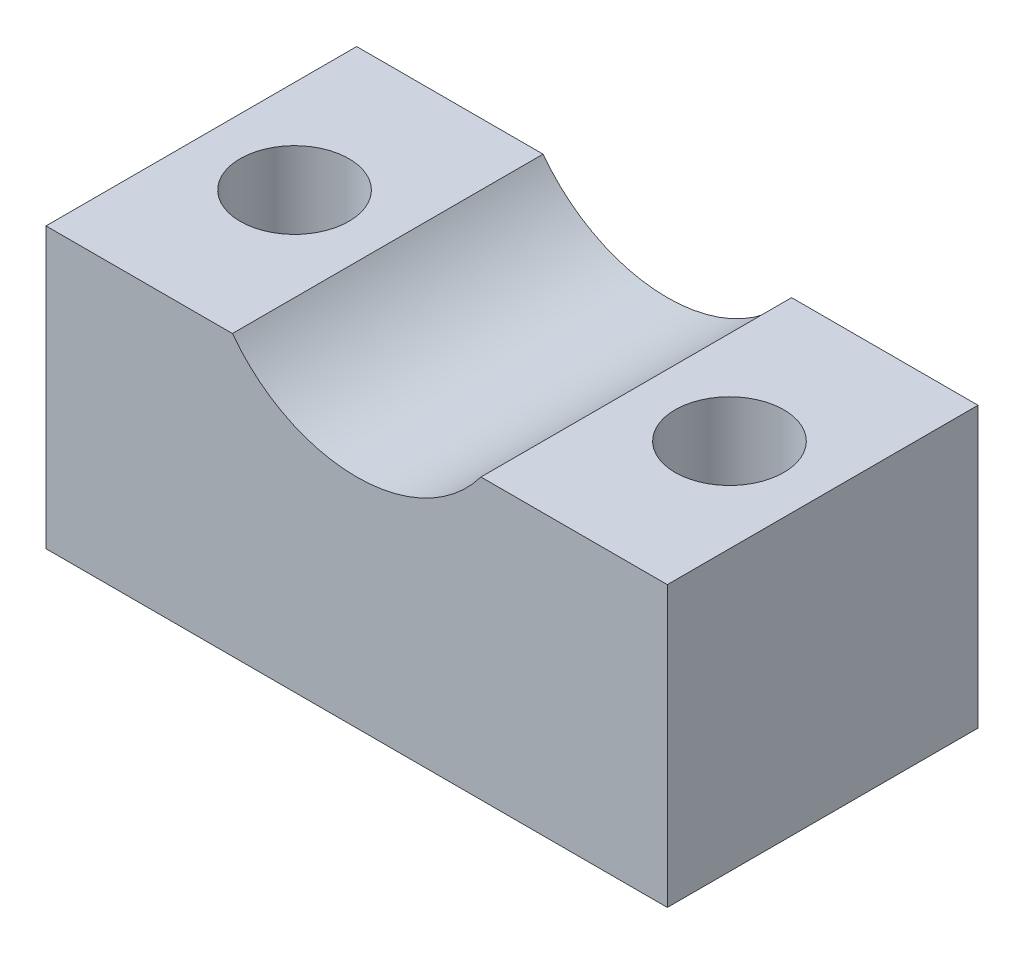
SolidWorks part; units mm, degrees
ref_plane "Ebene vorne" through (0, 0, 0) normal (0, 0, 1) x (1, 0, 0)
ref_plane "Ebene oben" through (0, 0, 0) normal (0, 1, 0) x (1, 0, 0)
ref_plane "Ebene rechts" through (0, 0, 0) normal (1, 0, 0) x (0, 0, -1)
sketch "Skizze1" plane through (0, 0, 0) normal (0, 0, 1) x (1, 0, 0)
  line L0 (0, 0) -> (20, 0)
  line L1 (20, 0) -> (20, 9)
  line L2 (20, 9) -> (14, 9)
  line L3 (0, 0) -> (0, 9)
  line L4 (0, 9) -> (6, 9)
  arc A0 (6, 9) -> (14, 9) centre (10, 12) ccw
  point P7 (10, 7)
  dimension "D1" = 6
  dimension "D2" = 6
  dimension "D3" = 2
  dimension "D4" = 9
  dimension "D5" = 20
  dimension "D6" = 0
  dimension "D7" = 0
  dimension "D8" = 0
extrude "Aufsatz-Linear austragen1" add sketch "Skizze1" along normal blind 10
sketch "Skizze2" plane through (0, 9, 0) normal (0, 1, 0) x (1, 0, 0)
  line L0 (6, 0) -> (0, 0) construction
  line L1 (0, -10) -> (0, 0) construction
  line L2 (20, -10) -> (20, 0) construction
  circle A0 centre (3, -5) radius 1.75
  circle A1 centre (17, -5) radius 1.75
  dimension "D5" = 3.5
  dimension "D6" = 3.5
  dimension "D1" = 5
  dimension "D2" = 0
  dimension "D3" = 3
  dimension "D4" = 3
extrude "Schnitt-Linear austragen1" cut sketch "Skizze2" against normal through all
